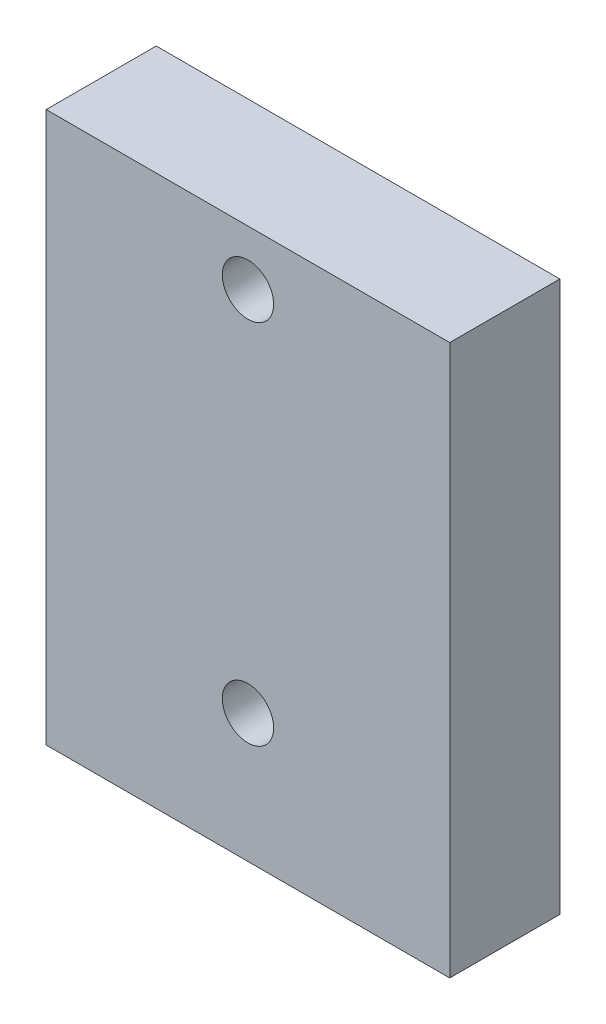
SolidWorks part; units mm, degrees
ref_plane "Plan de face" through (0, 0, 0) normal (0, 0, 1) x (1, 0, 0)
ref_plane "Plan de dessus" through (0, 0, 0) normal (0, 1, 0) x (1, 0, 0)
ref_plane "Plan de droite" through (0, 0, 0) normal (1, 0, 0) x (0, 0, -1)
sketch "Esquisse1" plane through (0, 0, 0) normal (0, 0, 1) x (1, 0, 0)
  line L1 (-15.3014, 15.393) -> (6.6986, 15.393)
  line L2 (-15.3014, 15.393) -> (-15.3014, -14.607)
  line L3 (-15.3014, -14.607) -> (6.6986, -14.607)
  line L4 (6.6986, 15.393) -> (6.6986, -14.607)
  circle A0 centre (-4.3014, 12.393) radius 1.4
  circle A1 centre (-4.3014, -7.607) radius 1.4
  dimension "D3" = 2.8
  dimension "D4" = 2.8
  dimension "D1" = 30
  dimension "D2" = 22
  dimension "D5" = 20
  dimension "D6" = 11
  dimension "D7" = 3
extrude "Boss.-Extru.1" add sketch "Esquisse1" along normal blind 6
